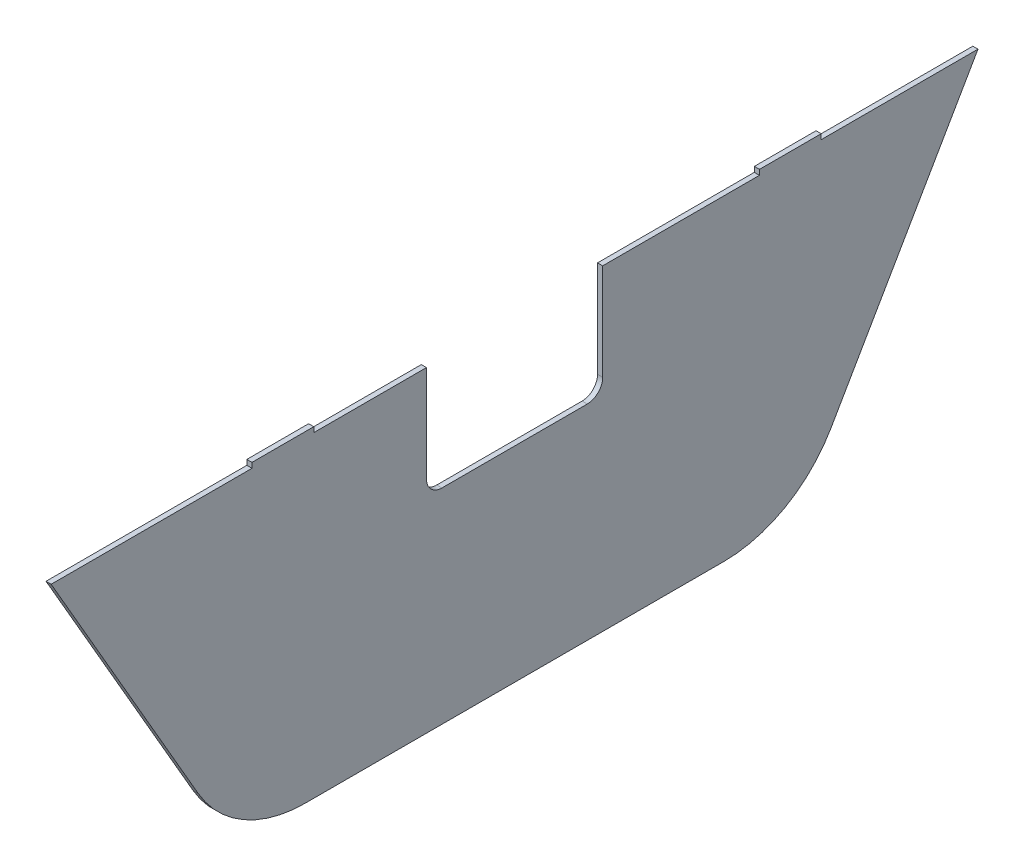
SolidWorks part; units mm, degrees
ref_plane "Front Plane" through (0, 0, 0) normal (0, 0, 1) x (1, 0, 0)
ref_plane "Top Plane" through (0, 0, 0) normal (0, 1, 0) x (1, 0, 0)
ref_plane "Right Plane" through (0, 0, 0) normal (1, 0, 0) x (0, 0, -1)
sketch "Sketch3" plane through (0, 0, 0) normal (1, 0, 0) x (0, 0, -1)
  line L0 (-58.8246, -2534.8065) -> (-1.6669, -2633.8065)
  line L1 (39.9023, -2657.8065) -> (202.4485, -2657.8065)
  line L2 (43.1754, -2534.8065) -> (86.9504, -2534.8065)
  line L3 (244.0177, -2633.8065) -> (301.1754, -2534.8065)
  line L6 (155.4004, -2534.8065) -> (155.4004, -2572.3065)
  line L7 (149.4004, -2578.3065) -> (92.9504, -2578.3065)
  line L8 (86.9504, -2572.3065) -> (86.9504, -2534.8065)
  line L9 (98.9504, -2546.8065) -> (98.9504, -2534.8065) construction
  line L10 (143.4004, -2546.8065) -> (143.4004, -2534.8065) construction
  line L11 (143.4004, -2657.8065) -> (98.9504, -2657.8065) construction
  line L12 (-58.8246, -2534.8065) -> (19.1754, -2534.8065)
  line L13 (155.4004, -2534.8065) -> (216.2879, -2534.8065)
  line L15 (19.1754, -2534.8065) -> (19.1754, -2532.8065)
  line L16 (19.1754, -2532.8065) -> (43.1754, -2532.8065)
  line L17 (43.1754, -2534.8065) -> (43.1754, -2532.8065)
  line L20 (216.2879, -2534.8065) -> (216.2879, -2532.8065)
  line L21 (216.2879, -2532.8065) -> (240.2879, -2532.8065)
  line L22 (240.2879, -2534.8065) -> (240.2879, -2532.8065)
  line L23 (240.2879, -2534.8065) -> (301.1754, -2534.8065)
  arc A0 (202.4485, -2657.8065) -> (244.0177, -2633.8065) centre (202.4485, -2609.8065) ccw
  arc A1 (-1.6669, -2633.8065) -> (39.9023, -2657.8065) centre (39.9023, -2609.8065) ccw
  circle A2 centre (135.1754, -2640.8065) radius 2.5 construction
  circle A3 centre (107.1754, -2640.8065) radius 2.5 construction
  circle A4 centre (135.1754, -2587.8065) radius 2.5 construction
  circle A5 centre (107.1754, -2587.8065) radius 2.5 construction
  circle A6 centre (135.1754, -2640.8065) radius 2.5
  circle A7 centre (107.1754, -2640.8065) radius 2.5
  circle A8 centre (135.1754, -2587.8065) radius 2.5
  circle A9 centre (107.1754, -2587.8065) radius 2.5
  arc A10 (111.3647, -2550.8065) -> (130.9861, -2550.8065) centre (121.1754, -2562.8065) ccw construction
  arc A11 (155.4004, -2572.3065) -> (149.4004, -2578.3065) centre (149.4004, -2572.3065) cw
  arc A12 (86.9504, -2572.3065) -> (92.9504, -2578.3065) centre (92.9504, -2572.3065) ccw
  point P11 (230.1613, -2657.8065)
  point P44 (31.1754, -2532.8065)
  dimension "D3" = 48
  dimension "D6" = 6
  dimension "D1" = 60
  dimension "D2" = 60
  dimension "D4" = 12
  dimension "D5" = 12
  dimension "D7" = 24
  dimension "D8" = 2
  dimension "D9" = 2
  dimension "D10" = 24
  dimension "D11" = 90
extrude "Boss-Extrude1" add sketch "Sketch3" along normal blind 2 contours L1 A0 L3 L23 L22 L21 L20 L13 L6 A11 L7 A12 L8 L2 L17 L16 L15 L12 L0 A1
